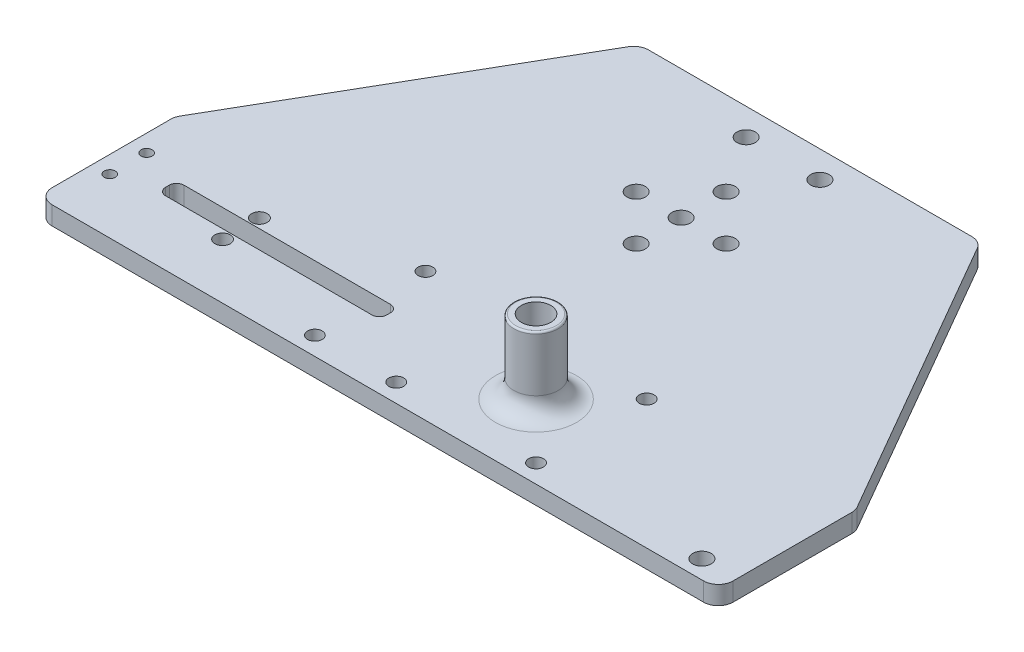
SolidWorks part; units mm, degrees
ref_plane "Front Plane" through (0, 0, 0) normal (0, 0, 1) x (1, 0, 0)
ref_plane "Top Plane" through (0, 0, 0) normal (0, 1, 0) x (1, 0, 0)
ref_plane "Right Plane" through (0, 0, 0) normal (1, 0, 0) x (0, 0, -1)
sketch "Sketch1" plane through (0, 0, 0) normal (0, 1, 0) x (1, 0, 0)
  line L0 (0, 0) -> (15, 0) construction
  line L6 (-96.298, -19.9924) -> (80.4548, -20)
  line L17 (-25, 0.5) -> (-25, -0.5)
  line L18 (-27, 2.5) -> (-83, 2.5)
  line L19 (-27, -2.5) -> (-83, -2.5)
  line L20 (-85, 0.5) -> (-85, -0.5)
  line L23 (-25, 0.5) -> (-25, -0.5)
  line L52 (84.4548, 16.2113) -> (84.4548, -16)
  line L53 (83.9189, 18.2113) -> (39.4215, 95.2831)
  line L54 (35.9574, 97.2831) -> (-51.7999, 97.2831)
  line L55 (-55.264, 95.2831) -> (-99.7614, 18.2113)
  line L60 (-100.2973, 16.2113) -> (-100.2973, -15.9924)
  line L62 (-54.1093, -62.7169) -> (-7.9212, -62.7169) [skipped]
  line L63 (-100.2973, 17.2831) -> (-95, 8.1079) [skipped]
  line L64 (61.3608, -22.7169) -> (62.9294, -20) [skipped]
  arc A0 (-27, -2.5) -> (-25, -0.5) centre (-27, -0.5) ccw
  arc A1 (-83, -2.5) -> (-85, -0.5) centre (-83, -0.5) cw
  arc A3 (-25, 0.5) -> (-27, 2.5) centre (-27, 0.5) ccw
  arc A4 (-83, 2.5) -> (-85, 0.5) centre (-83, 0.5) ccw
  circle A14 centre (15, 0) radius 4
  arc A15 (39.4215, 95.2831) -> (35.9574, 97.2831) centre (35.9574, 93.2831) ccw
  arc A16 (83.9189, 18.2113) -> (84.4548, 16.2113) centre (80.4548, 16.2113) cw
  arc A17 (84.4548, -16) -> (80.4548, -20) centre (80.4548, -16) cw
  arc A19 (-99.7614, 18.2113) -> (-100.2973, 16.2113) centre (-96.2973, 16.2113) ccw
  arc A20 (-51.7999, 97.2831) -> (-55.264, 95.2831) centre (-51.7999, 93.2831) ccw
  arc A21 (-100.2973, -15.9924) -> (-96.298, -19.9924) centre (-96.2973, -15.9924) ccw
  point P0 (0, 0)
  dimension "D1" = 2
  dimension "D3" = 4
extrude "Boss-Extrude1" add sketch "Sketch1" along normal blind 5
sketch "Sketch2" plane through (0, 5, 0) normal (0, 1, 0) x (1, 0, 0)
  circle A0 centre (15, 0) radius 6
  circle A1 centre (15, 0) radius 4
extrude "Boss-Extrude2" add sketch "Sketch2" along normal blind 20
fillet "Fillet1" radius 5 1 edges at (15, 5, 6)
fillet "Fillet2" radius 0.5 1 edges at (15, 25, 6)
sketch "Sketch3" plane through (0, 5, 0) normal (0, 1, 0) x (1, 0, 0)
  circle A0 centre (-30, 15) radius 2
  circle A1 centre (-30, -15) radius 2
extrude "Cut-Extrude3" cut sketch "Sketch3" against normal up to next (5 mm away)
mirror "Mirror1" about plane through (0, 0, 0) normal (1, 0, 0) of "Cut-Extrude3"
sketch "Sketch10" plane through (0, 0, 0) normal (0, -1, 0) x (1, 0, 0)
  circle A8 centre (-18, -90) radius 2.5
  circle A9 centre (2, -90) radius 2.5
extrude "Cut-Extrude8" cut sketch "Sketch10" against normal up to next
sketch "Sketch13" plane through (0, 0, 0) normal (0, -1, 0) x (-1, 0, 0)
  circle A0 centre (95.6473, -4.9924) radius 1.5
  circle A1 centre (95.6473, 5.0076) radius 1.5
extrude "Cut-Extrude10" cut sketch "Sketch13" against normal up to next
sketch "Sketch14" plane through (0, 0, 0) normal (0, -1, 0) x (1, 0, 0)
  circle A0 centre (-65.0473, 4.9924) radius 2.1
  circle A1 centre (-65.0473, -5.0076) radius 2.1
extrude "Cut-Extrude11" cut sketch "Sketch14" against normal up to next
sketch "Sketch15" plane through (0, 0, 0) normal (0, -1, 0) x (-1, 0, 0)
  circle A0 centre (7.9212, 62.2831) radius 18.75
hole_wizard "Ø5.0mm Dowel Hole1" positions "3DSketch1" profile "Sketch16" hole size "Ø5.0" standard "ANSI Metric"
sketch3d "3DSketch1"
  point P0 (-7.9212, 0, -62.2831)
sketch "Sketch16" plane through (-7.9212, 0, -62.2831) normal (1, 0, 0) x (0, 0, -1)
  line L0 (0, 0) -> (0, 9.0022)
  line L1 (0, 9.0022) -> (2.5, 7.5)
  line L2 (2.5, 7.5) -> (2.5, 0)
  line L5 (2.5, 0) -> (0, 0)
  line L10 (0, 9.0022) -> (-2.5, 7.5) construction
  line L11 (0, -6.35) -> (0, 107.95) construction
  dimension "Hole Dia." = 5
  dimension "Hole Depth" = 7.5
  dimension "Drill Angle" = 118
pattern_linear "LPattern1" count 2 spacing 12.2 along (1, 0, 0) of "Ø5.0mm Dowel Hole1"
pattern_circular "CirPattern1" count 4 every 90 about axis through (-7.9212, 0, -62.2831) along (0, 1, 0) of "LPattern1"
sketch "Sketch17" plane through (0, 5, 0) normal (0, 1, 0) x (1, 0, 0)
  line L0 (-96.298, -19.9924) -> (80.4548, -20) construction
  line L1 (-100.2973, 16.2113) -> (-100.2973, -15.9924) construction
  point P0 (-7.9223, -14.9962)
  dimension "D1" = 5
  dimension "D2" = 92.375
hole_wizard "Ø4.0mm Dowel Hole1" positions "Sketch18" profile "Sketch19" hole size "Ø4.0" standard "ANSI Metric" end condition up to next
sketch "Sketch18" plane through (0, 5, 0) normal (0, 1, 0) x (1, 0, 0)
  point P0 (-7.9223, -14.9962)
sketch "Sketch19" plane through (-7.9223, 5, 14.9962) normal (1, 0, 0) x (0, 0, 1)
  line L0 (0, 0) -> (0, 5)
  line L1 (0, 5) -> (2, 5)
  line L2 (2, 5) -> (2, 0)
  line L5 (2, 0) -> (0, 0)
  line L11 (0, -6.35) -> (0, 107.95) construction
  dimension "Thru Hole Dia." = 4
  dimension "Thru Hole Depth" = 5
sketch "Sketch20" plane through (0, 5, 0) normal (0, 1, 0) x (1, 0, 0)
  circle A0 centre (75, -15) radius 2.5
extrude "Cut-Extrude12" cut sketch "Sketch20" against normal blind 10 contours A0
